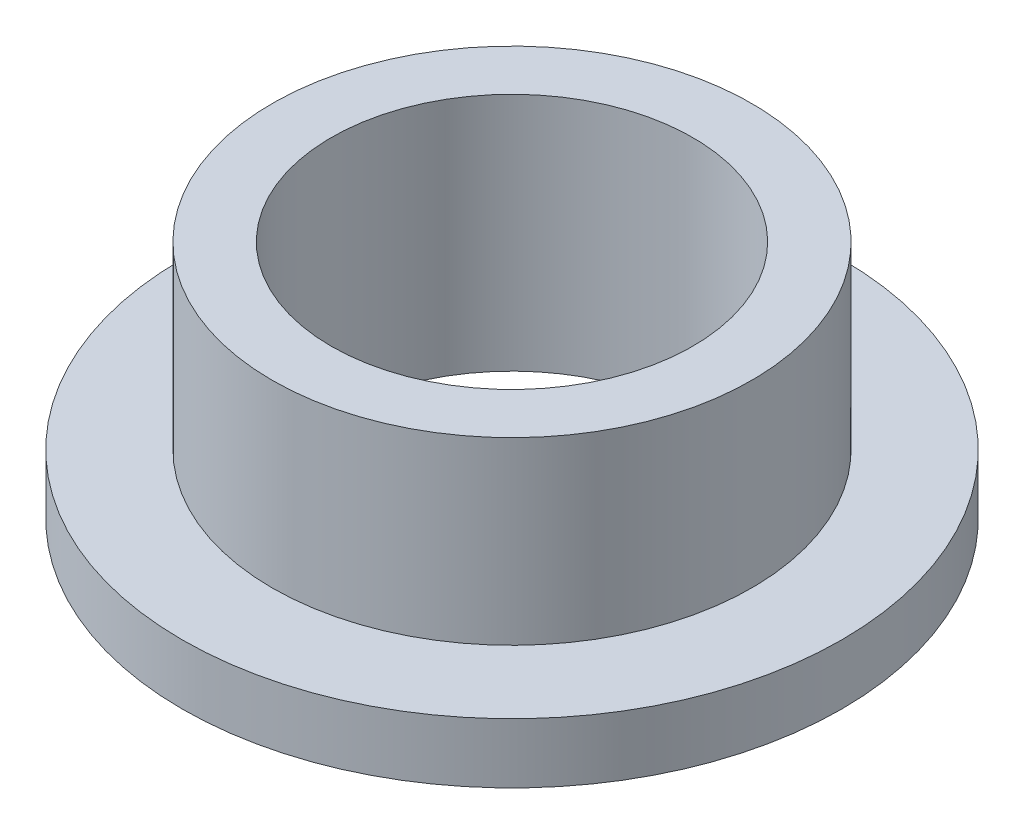
SolidWorks part; units mm, degrees
ref_plane "Front" through (0, 0, 0) normal (0, 0, 1) x (1, 0, 0)
ref_plane "Top" through (0, 0, 0) normal (0, 1, 0) x (1, 0, 0)
ref_plane "Right" through (0, 0, 0) normal (1, 0, 0) x (0, 0, -1)
sketch "Sketch1" plane through (0, 0, 0) normal (0, 1, 0) x (1, 0, 0)
  circle A0 centre (0, 0) radius 4.7879
  circle A1 centre (0, 0) radius 6.35
  circle A2 centre (0, 0) radius 7.9375
  dimension "ID" = 9.5758
  dimension "OD" = 12.7
  dimension "FlangeOD" = 15.875
sketch "Sketch2" plane through (0, 0, 0) normal (0, 1, 0) x (1, 0, 0)
  circle A0 centre (0, 0) radius 4.7879 construction
  circle A1 centre (0, 0) radius 6.35 construction
  circle A2 centre (0, 0) radius 4.7879
  circle A3 centre (0, 0) radius 6.35
extrude "Boss-Extrude1" add sketch "Sketch2" along normal blind 6.35
sketch "Sketch3" plane through (0, 0, 0) normal (0, 1, 0) x (1, 0, 0)
  circle A1 centre (0, 0) radius 6.35 construction
  circle A2 centre (0, 0) radius 8.7312
  circle A3 centre (0, 0) radius 6.35
  dimension "D1" = 17.4625
extrude "Boss-Extrude2" add sketch "Sketch3" along normal blind 1.5875
